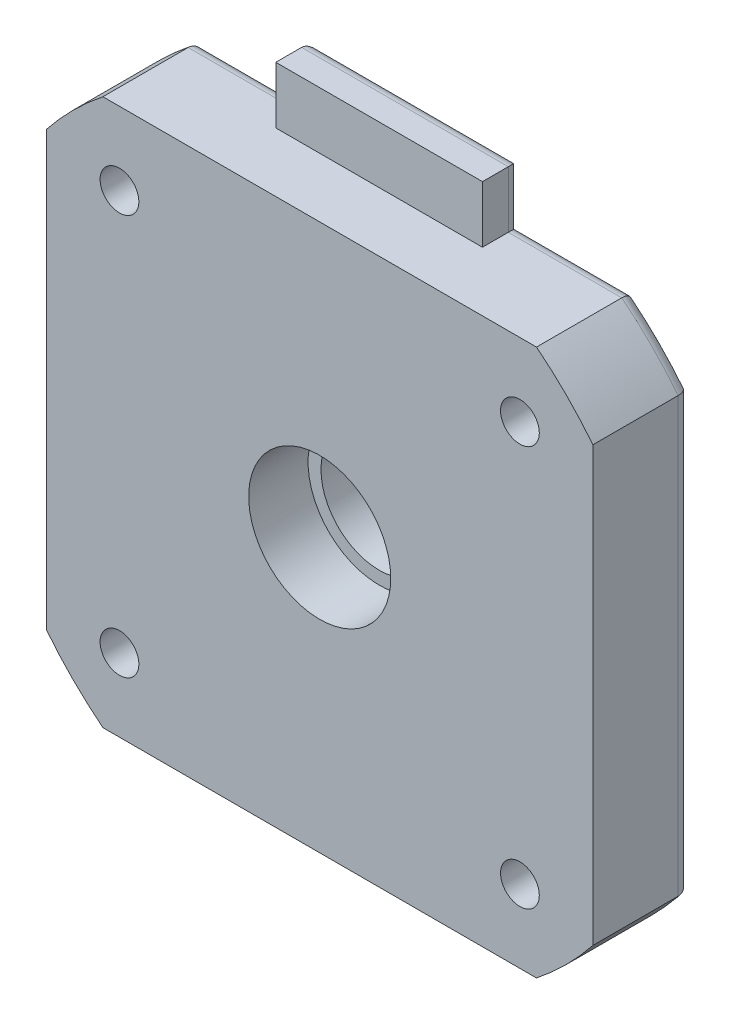
SolidWorks part; units mm, degrees
material "Acero aleado"
ref_plane "Alzado" through (0, 0, 0) normal (0, 0, 1) x (1, 0, 0)
ref_plane "Planta" through (0, 0, 0) normal (0, 1, 0) x (1, 0, 0)
ref_plane "Vista lateral" through (0, 0, 0) normal (1, 0, 0) x (0, 0, -1)
sketch "Croquis1" plane through (0, 0, 0) normal (0, 0, 1) x (1, 0, 0)
  line L0 (-21.15, 21.15) -> (21.15, 21.15)
  line L1 (-21.15, -21.15) -> (21.15, -21.15)
  line L2 (-21.15, 21.15) -> (-21.15, -21.15)
  line L4 (21.15, 21.15) -> (21.15, -21.15)
  line L5 (-21.15, 21.15) -> (21.15, -21.15) construction
  line L6 (-21.15, -21.15) -> (21.15, 21.15) construction
  point P0 (0, 0)
  dimension "D1" = 42.3
  dimension "D2" = 42.3
extrude "Extrude Feature" add sketch "Croquis1" along normal blind 7.6
sketch "Sketch2" plane through (0, 0, 7.6) normal (0, 0, 1) x (1, 0, 0)
  circle A0 centre (0, 0) radius 27
  circle A1 centre (0, 0) radius 29.9106
  dimension "D1" = 54
extrude "Cut-Extrude1" cut sketch "Sketch2" against normal through all
sketch "Croquis5" plane through (0, 0, 0) normal (0, 0, -1) x (-1, 0, 0)
  circle A0 centre (-15.5, 15.5) radius 1.5
  circle A1 centre (15.5, 15.5) radius 1.5
  circle A2 centre (15.5, -15.5) radius 1.5
  circle A3 centre (-15.5, -15.5) radius 1.5
  point P12 (0, 0)
  dimension "D1" = 3
  dimension "D2" = 15.5
  dimension "D3" = 15.5
  dimension "D5" = 31
  dimension "D6" = 15.5
  dimension "D4" = 4
extrude "Cortar-Extruir2" cut sketch "Croquis5" against normal blind 22
sketch "Croquis6" plane through (0, 0, 0) normal (0, 0, -1) x (-1, 0, 0)
  circle A0 centre (0, 0) radius 4.5
  dimension "D1" = 9
extrude "Cortar-Extruir3" cut sketch "Croquis6" against normal through all
sketch "Sketch3" plane through (0, 0, 7.6) normal (0, 0, 1) x (1, 0, 0)
  circle A0 centre (0, 0) radius 5.5
  dimension "D1" = 11
extrude "Cut-Extrude2" cut sketch "Sketch3" against normal offset from surface (4.6 mm away) 3 up to face at (-4.5, 0, 0)
sketch "Croquis7" plane through (0, 0, 0) normal (0, 0, -1) x (-1, 0, 0)
  circle A0 centre (-15.5, 15.5) radius 3
  circle A1 centre (15.5, 15.5) radius 3
  circle A2 centre (15.5, -15.5) radius 3
  circle A3 centre (-15.5, -15.5) radius 3
  dimension "D1" = 6
  dimension "D2" = 4
extrude "Cortar-Extruir4" cut sketch "Croquis7" against normal blind 3
sketch "Sketch1" plane through (0, 0, 0) normal (0, 0, -1) x (-1, 0, 0)
  line L1 (-8, 25.55) -> (8, 25.55)
  line L2 (-8, 25.55) -> (-8, 21.15)
  line L3 (-8, 21.15) -> (8, 21.15)
  line L4 (8, 25.55) -> (8, 21.15)
  line L5 (-8, 25.55) -> (8, 21.15) construction
  line L6 (-8, 21.15) -> (8, 25.55) construction
  line L7 (-16.7833, 21.15) -> (16.7833, 21.15) construction
  point P0 (0, 23.35)
  dimension "D1" = 16
  dimension "D2" = 4.4
extrude "Boss-Extrude1" add sketch "Sketch1" against normal blind 3
fillet "Fillet1" radius 1 12 edges at (-19.0919, 19.0919, 0) (-21.15, 0, 0) (-19.0919, -19.0919, 0) (0, -21.15, 0) (19.0919, -19.0919, 0) (21.15, 0, 0) (19.0919, 19.0919, 0) (-8, 23.35, 0) (0, 25.55, 0) (-12.3916, 21.15, 0) (8, 23.35, 0) (12.3916, 21.15, 0)
chamfer "Chamfer1" distance 0.5 angle 45 4 edges at (-18.5, -15.5, 0) (12.5, -15.5, 0) (-18.5, 15.5, 0) (12.5, 15.5, 0)
